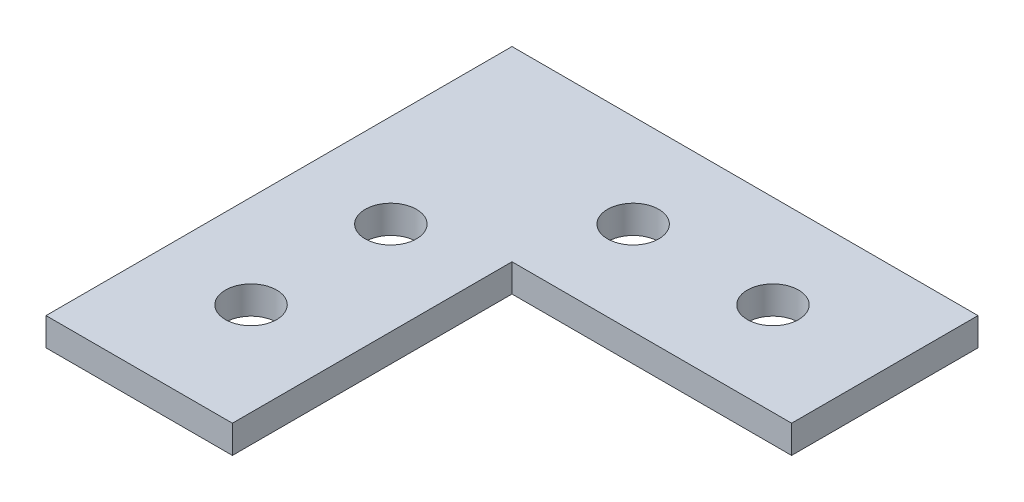
SolidWorks part; units mm, degrees
ref_plane "Front Plane" through (0, 0, 0) normal (0, 0, 1) x (1, 0, 0)
ref_plane "Top Plane" through (0, 0, 0) normal (0, 1, 0) x (1, 0, 0)
ref_plane "Right Plane" through (0, 0, 0) normal (1, 0, 0) x (0, 0, -1)
sketch "Sketch1" plane through (0, 0, 0) normal (0, 1, 0) x (1, 0, 0)
  line L1 (0, 0) -> (20, 0)
  line L2 (0, 0) -> (0, -50)
  line L3 (0, -50) -> (20, -50)
  line L4 (20, 0) -> (20, -50)
  line L5 (20, 0) -> (50, 0)
  line L7 (20, -20) -> (50, -20)
  line L8 (50, 0) -> (50, -20)
  dimension "D1" = 50
  dimension "D2" = 20
  dimension "D3" = 20
  dimension "D4" = 30
extrude "Boss-Extrude1" add sketch "Sketch1" along normal blind 3 contours L4 L1 L2 L3 | L8 L5 L4 L7
sketch "Sketch3" plane through (0, 3, 0) normal (0, 1, 0) x (1, 0, 0)
  line L0 (10, -50) -> (10, 0) construction
  line L1 (0, -50) -> (20, -50) construction
  line L2 (0, 0) -> (50, 0) construction
  line L3 (50, -10) -> (0, -10) construction
  line L4 (50, 0) -> (50, -20) construction
  line L5 (0, 0) -> (0, -50) construction
  circle A0 centre (10, -38) radius 2.75
  circle A1 centre (10, -23) radius 2.75
  circle A2 centre (38, -10) radius 2.75
  circle A3 centre (23, -10) radius 2.75
  point P22 (6.3216, -35.1663)
  dimension "D1" = 5.5
  dimension "D2" = 5.5
  dimension "D5" = 5.5
  dimension "D6" = 5.5
  dimension "D3" = 12
  dimension "D4" = 15
  dimension "D7" = 12
  dimension "D8" = 15
extrude "Cut-Extrude1" cut sketch "Sketch3" against normal blind 3
